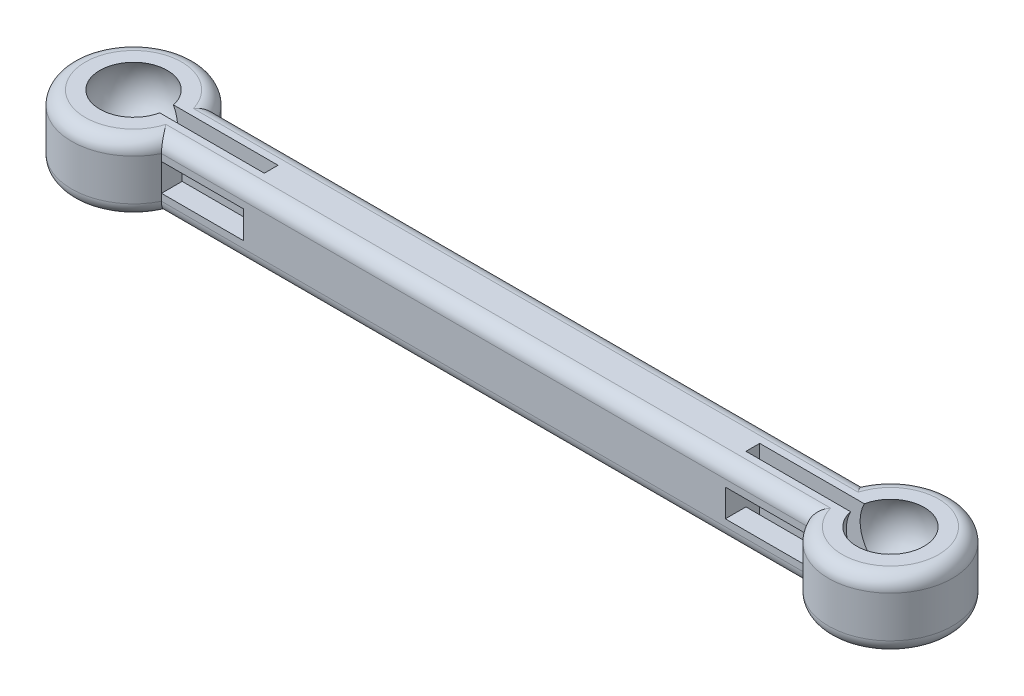
SolidWorks part; units mm, degrees
ref_plane "Front Plane" through (0, 0, 0) normal (0, 0, 1) x (1, 0, 0)
ref_plane "Top Plane" through (0, 0, 0) normal (0, 1, 0) x (1, 0, 0)
ref_plane "Right Plane" through (0, 0, 0) normal (1, 0, 0) x (0, 0, -1)
sketch "Sketch1" plane through (0, 0, 0) normal (0, 1, 0) x (1, 0, 0)
  line L1 (-27.5, -2) -> (27.5, -2)
  line L2 (-27.5, -2) -> (-27.5, 2)
  line L3 (-27.5, 2) -> (27.5, 2)
  line L4 (27.5, -2) -> (27.5, 2)
  line L5 (-27.5, -2) -> (27.5, 2) construction
  line L6 (-27.5, 2) -> (27.5, -2) construction
  circle A0 centre (27.5, 0) radius 4.5
  circle A1 centre (-27.5, 0) radius 4.5
  point P0 (0, 0)
  point P4 (0, 0)
  dimension "D2" = 9
  dimension "D1" = 55
  dimension "D3" = 4
extrude "Boss-Extrude1" add sketch "Sketch1" along normal blind 5 contours L3 A1 L1 L2 | L1 A1 L3 L2 | A1 L1 A0 L3 | L3 A0 L1 L4 | L1 A0 L3 L4
sketch3d "3DSketch1"
  line L0 (-27.5, 5, 0) -> (-27.5, 6.5, 0)
  line L1 (-27.5, 5, 0) -> (-27.5, 1, 0)
  arc A0 (-23.4689, 5, -2) -> (-23.4689, 5, 2) centre (-27.5, 5, 0) ccw construction
  arc A1 (-27.5, 1, 0) -> (-27.5, 6.5, 0) centre (-27.5, 3.75, 0) cw
  point P3 (-30.25, 3.75, 0)
  point P7 (-27.5, 9.5, 0)
  dimension "D1" = 4
  dimension "D2" = 1.5
sketch "Sketch2" plane through (0, 5, 0) normal (0, 1, 0) x (1, 0, 0)
  circle A0 centre (-27.5, 0) radius 4.5
  arc A1 (-23.4689, 2) -> (-23.4689, -2) centre (-27.5, 0) ccw construction
sweep "Cut-Sweep1" cut profiles "3DSketch1" path "Sketch2"
mirror "Mirror1" about plane through (0, 0, 0) normal (1, 0, 0) of "Cut-Sweep1"
sketch "Sketch3" plane through (0, 0, 0) normal (0, -1, 0) x (1, 0, 0)
  line L0 (-23.4689, 2) -> (23.4689, 2) construction
  line L1 (-27.5, 0) -> (-17.5, 0)
  line L2 (-27.5, 0) -> (-27.5, 0.5)
  line L3 (-27.5, 0.5) -> (-17.5, 0.5)
  line L4 (-17.5, 0) -> (-17.5, 0.5)
  line L5 (-27.5, 0) -> (-17.5, 0)
  line L6 (-27.5, 0) -> (-27.5, -0.5)
  line L7 (-27.5, -0.5) -> (-17.5, -0.5)
  line L8 (-17.5, 0) -> (-17.5, -0.5)
  circle A0 centre (-27.5, 0) radius 4.5
  arc A1 (-23.4689, 2) -> (-23.4689, -2) centre (-27.5, 0) ccw construction
  dimension "D1" = 1.5
  dimension "D2" = 10
extrude "Cut-Extrude1" cut sketch "Sketch3" against normal up to surface (5 mm away) contours A0 L5 L4 L3 | A0 L7 L8 L5 | L1 A0 L3 L2 | L7 A0 L1 L6 up to face at (27.5, 5, 2.4495)
mirror "Mirror2" about plane through (0, 0, 0) normal (1, 0, 0) of "Cut-Extrude1"
sketch "Sketch4" plane through (0, 0, -2) normal (0, 0, -1) x (-1, 0, 0)
  line L0 (23.4689, 0) -> (17.5, 5)
  line L2 (23.4689, 5) -> (-23.4689, 5) construction
  line L3 (23.4689, 5) -> (23.4689, 0) construction
  line L4 (23.4689, 3.5) -> (17.5, 3.5)
  line L5 (23.4689, 3.5) -> (23.4689, 1.5)
  line L6 (23.4689, 1.5) -> (17.5, 1.5)
  line L7 (17.5, 3.5) -> (17.5, 1.5)
  line L8 (23.4689, 3.5) -> (17.5, 1.5) construction
  line L9 (23.4689, 1.5) -> (17.5, 3.5) construction
  point P6 (20.4844, 2.5)
  line M6 (23.4689, 0) -> (23.4689, 5)
  dimension "D1" = 2
extrude "Cut-Extrude2" cut sketch "Sketch4" against normal up to surface (4 mm away) contours L4 L7 L6 L0 | L6 L4 L0 M6 up to face at (0, 2.5, 2)
mirror "Mirror3" about plane through (0, 0, 0) normal (1, 0, 0) of "Cut-Extrude2"
fillet "Fillet1" radius 1 4 edges at (0, 5, 2) (0, 5, -2) (32, 5, 0) (-32, 5, 0)
fillet "Fillet2" radius 1 4 edges at (0, 0, 2) (32, 0, 0) (-32, 0, 0) (0, 0, -2)
